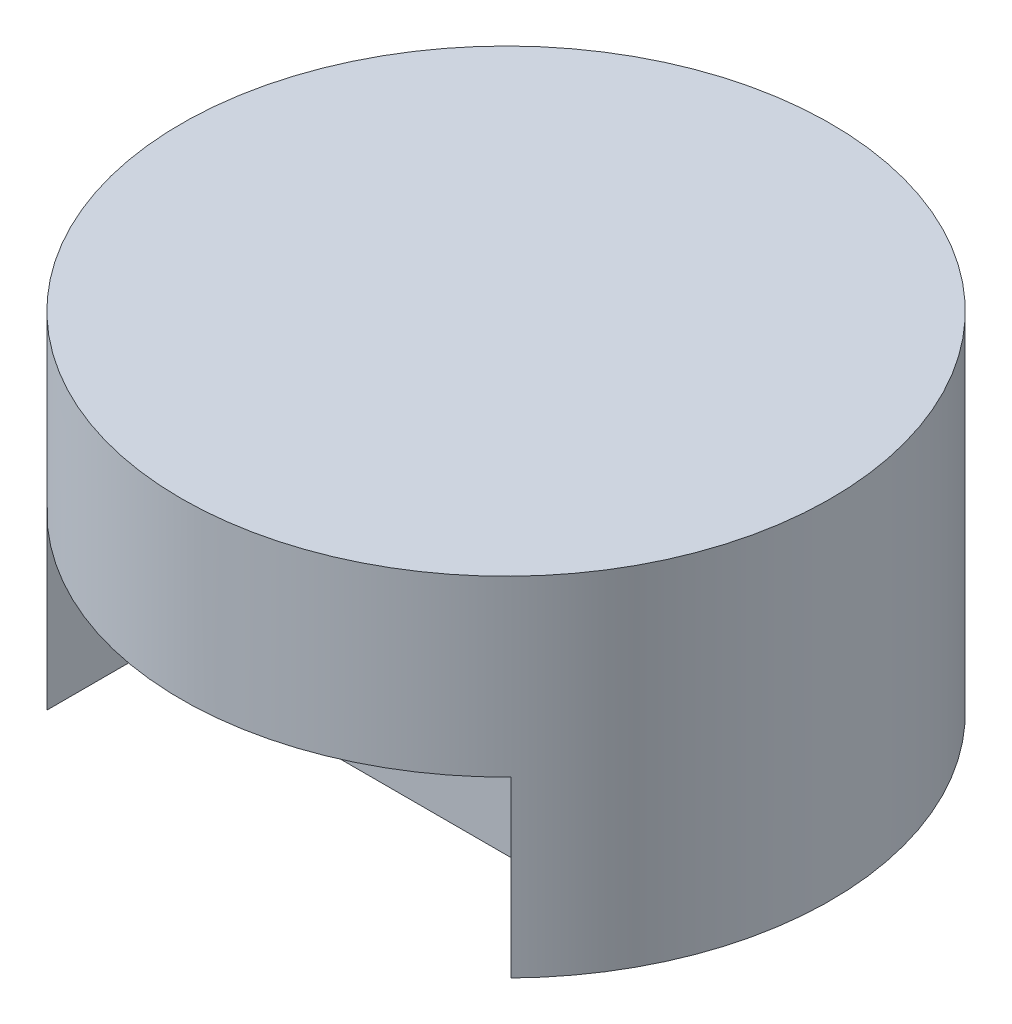
SolidWorks part; units mm, degrees
ref_plane "Front Plane" through (0, 0, 0) normal (0, 0, 1) x (1, 0, 0)
ref_plane "Top Plane" through (0, 0, 0) normal (0, 1, 0) x (1, 0, 0)
ref_plane "Right Plane" through (0, 0, 0) normal (1, 0, 0) x (0, 0, -1)
sketch "Sketch1" plane through (0, 0, 0) normal (0, 1, 0) x (1, 0, 0)
  circle A0 centre (0, 0) radius 140
  dimension "D1" = 280
extrude "Boss-Extrude1" add sketch "Sketch1" along normal blind 150
sketch "Sketch2" plane through (0, 0, 0) normal (0, -1, 0) x (1, 0, 0)
  line L0 (-100, 97.9796) -> (-100, 52.9796)
  line L1 (-100, 52.9796) -> (100, 52.9796)
  line L2 (0, 140) -> (0, 0) construction
  line L3 (100, 97.9796) -> (100, 52.9796)
  circle A0 centre (0, 0) radius 140 construction
  arc A1 (-100, 97.9796) -> (100, 97.9796) centre (0, 0) cw
  point P10 (0, 52.9796)
  dimension "D1" = 45
  dimension "D2" = 200
extrude "Cut-Extrude1" cut sketch "Sketch2" against normal blind 75
